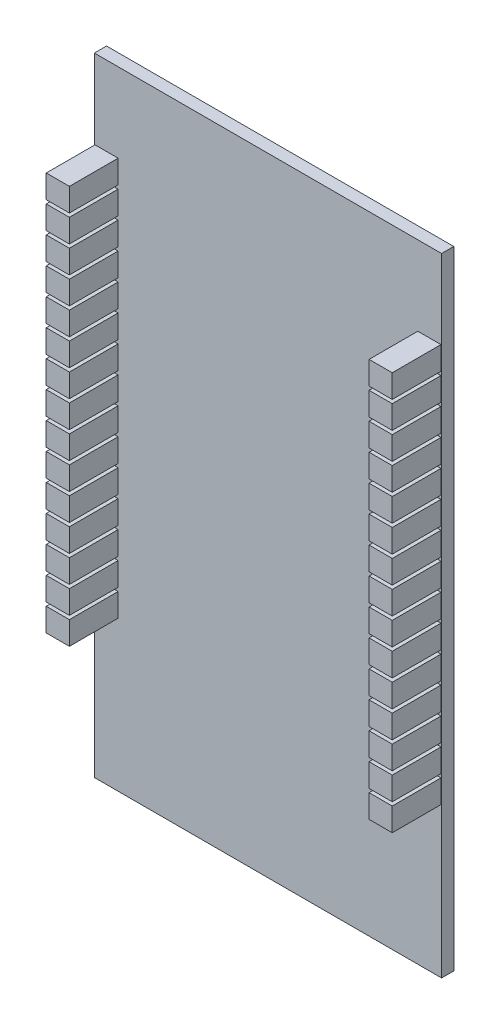
SolidWorks part; units mm, degrees
material "ﾎﾟﾘﾌﾟﾛﾋﾟﾚﾝ ﾎﾓﾎﾟﾘﾏｰ(PP Homopolymer)"
ref_plane "正面" through (0, 0, 0) normal (0, 0, 1) x (1, 0, 0)
ref_plane "平面" through (0, 0, 0) normal (0, 1, 0) x (1, 0, 0)
ref_plane "右側面" through (0, 0, 0) normal (1, 0, 0) x (0, 0, -1)
sketch "ｽｹｯﾁ1" plane through (0, 0, 0) normal (0, 0, 1) x (1, 0, 0)
  line L1 (0, 0) -> (28.5, 0)
  line L2 (0, 0) -> (0, 51.5)
  line L3 (0, 51.5) -> (28.5, 51.5)
  line L4 (28.5, 0) -> (28.5, 51.5)
  dimension "D1" = 28.5
  dimension "D2" = 51.5
extrude "ﾎﾞｽ - 押し出し1" add sketch "ｽｹｯﾁ1" along normal blind 1
sketch "ｽｹｯﾁ2" plane through (0, 0, 1) normal (0, 0, 1) x (1, 0, 0)
  line L0 (14.25, 0) -> (14.25, 51.5) construction
  line L1 (0.05, 45) -> (1.95, 45)
  line L2 (0.05, 45) -> (0.05, 43.1)
  line L3 (0.05, 43.1) -> (1.95, 43.1)
  line L4 (1.95, 45) -> (1.95, 43.1)
  line L5 (0, 51.5) -> (0, 0) construction
  line L6 (28.5, 51.5) -> (0, 51.5) construction
  line L7 (0, 0) -> (28.5, 0) construction
  line L8 (28.45, 45) -> (28.45, 43.1)
  line L9 (28.45, 43.1) -> (26.55, 43.1)
  line L10 (26.55, 45) -> (26.55, 43.1)
  line L11 (28.45, 45) -> (26.55, 45)
  line L12 (0.05, 42.8) -> (1.95, 42.8)
  line L13 (0.05, 42.8) -> (0.05, 40.9)
  line L14 (1.95, 42.8) -> (1.95, 40.9)
  line L15 (0.05, 40.9) -> (1.95, 40.9)
  line L16 (28.45, 42.8) -> (26.55, 42.8)
  line L17 (26.55, 42.8) -> (26.55, 40.9)
  line L18 (28.45, 42.8) -> (28.45, 40.9)
  line L19 (28.45, 40.9) -> (26.55, 40.9)
  line L20 (0.05, 40.6) -> (1.95, 40.6)
  line L21 (0.05, 40.6) -> (0.05, 38.7)
  line L22 (1.95, 40.6) -> (1.95, 38.7)
  line L23 (0.05, 38.7) -> (1.95, 38.7)
  line L24 (28.45, 40.6) -> (26.55, 40.6)
  line L25 (26.55, 40.6) -> (26.55, 38.7)
  line L26 (28.45, 40.6) -> (28.45, 38.7)
  line L27 (28.45, 38.7) -> (26.55, 38.7)
  line L28 (0.05, 38.4) -> (1.95, 38.4)
  line L29 (0.05, 38.4) -> (0.05, 36.5)
  line L30 (1.95, 38.4) -> (1.95, 36.5)
  line L31 (0.05, 36.5) -> (1.95, 36.5)
  line L32 (28.45, 38.4) -> (26.55, 38.4)
  line L33 (26.55, 38.4) -> (26.55, 36.5)
  line L34 (28.45, 38.4) -> (28.45, 36.5)
  line L35 (28.45, 36.5) -> (26.55, 36.5)
  line L36 (0.05, 36.2) -> (1.95, 36.2)
  line L37 (0.05, 36.2) -> (0.05, 34.3)
  line L38 (1.95, 36.2) -> (1.95, 34.3)
  line L39 (0.05, 34.3) -> (1.95, 34.3)
  line L40 (28.45, 36.2) -> (26.55, 36.2)
  line L41 (26.55, 36.2) -> (26.55, 34.3)
  line L42 (28.45, 36.2) -> (28.45, 34.3)
  line L43 (28.45, 34.3) -> (26.55, 34.3)
  line L44 (0.05, 34) -> (1.95, 34)
  line L45 (0.05, 34) -> (0.05, 32.1)
  line L46 (1.95, 34) -> (1.95, 32.1)
  line L47 (0.05, 32.1) -> (1.95, 32.1)
  line L48 (28.45, 34) -> (26.55, 34)
  line L49 (26.55, 34) -> (26.55, 32.1)
  line L50 (28.45, 34) -> (28.45, 32.1)
  line L51 (28.45, 32.1) -> (26.55, 32.1)
  line L52 (0.05, 31.8) -> (1.95, 31.8)
  line L53 (0.05, 31.8) -> (0.05, 29.9)
  line L54 (1.95, 31.8) -> (1.95, 29.9)
  line L55 (0.05, 29.9) -> (1.95, 29.9)
  line L56 (28.45, 31.8) -> (26.55, 31.8)
  line L57 (26.55, 31.8) -> (26.55, 29.9)
  line L58 (28.45, 31.8) -> (28.45, 29.9)
  line L59 (28.45, 29.9) -> (26.55, 29.9)
  line L60 (0.05, 29.6) -> (1.95, 29.6)
  line L61 (0.05, 29.6) -> (0.05, 27.7)
  line L62 (1.95, 29.6) -> (1.95, 27.7)
  line L63 (0.05, 27.7) -> (1.95, 27.7)
  line L64 (28.45, 29.6) -> (26.55, 29.6)
  line L65 (26.55, 29.6) -> (26.55, 27.7)
  line L66 (28.45, 29.6) -> (28.45, 27.7)
  line L67 (28.45, 27.7) -> (26.55, 27.7)
  line L68 (0.05, 27.4) -> (1.95, 27.4)
  line L69 (0.05, 27.4) -> (0.05, 25.5)
  line L70 (1.95, 27.4) -> (1.95, 25.5)
  line L71 (0.05, 25.5) -> (1.95, 25.5)
  line L72 (28.45, 27.4) -> (26.55, 27.4)
  line L73 (26.55, 27.4) -> (26.55, 25.5)
  line L74 (28.45, 27.4) -> (28.45, 25.5)
  line L75 (28.45, 25.5) -> (26.55, 25.5)
  line L76 (0.05, 25.2) -> (1.95, 25.2)
  line L77 (0.05, 25.2) -> (0.05, 23.3)
  line L78 (1.95, 25.2) -> (1.95, 23.3)
  line L79 (0.05, 23.3) -> (1.95, 23.3)
  line L80 (28.45, 25.2) -> (26.55, 25.2)
  line L81 (26.55, 25.2) -> (26.55, 23.3)
  line L82 (28.45, 25.2) -> (28.45, 23.3)
  line L83 (28.45, 23.3) -> (26.55, 23.3)
  line L84 (0.05, 23) -> (1.95, 23)
  line L85 (0.05, 23) -> (0.05, 21.1)
  line L86 (1.95, 23) -> (1.95, 21.1)
  line L87 (0.05, 21.1) -> (1.95, 21.1)
  line L88 (28.45, 23) -> (26.55, 23)
  line L89 (26.55, 23) -> (26.55, 21.1)
  line L90 (28.45, 23) -> (28.45, 21.1)
  line L91 (28.45, 21.1) -> (26.55, 21.1)
  line L92 (0.05, 20.8) -> (1.95, 20.8)
  line L93 (0.05, 20.8) -> (0.05, 18.9)
  line L94 (1.95, 20.8) -> (1.95, 18.9)
  line L95 (0.05, 18.9) -> (1.95, 18.9)
  line L96 (28.45, 20.8) -> (26.55, 20.8)
  line L97 (26.55, 20.8) -> (26.55, 18.9)
  line L98 (28.45, 20.8) -> (28.45, 18.9)
  line L99 (28.45, 18.9) -> (26.55, 18.9)
  line L100 (0.05, 18.6) -> (1.95, 18.6)
  line L101 (0.05, 18.6) -> (0.05, 16.7)
  line L102 (1.95, 18.6) -> (1.95, 16.7)
  line L103 (0.05, 16.7) -> (1.95, 16.7)
  line L104 (28.45, 18.6) -> (26.55, 18.6)
  line L105 (26.55, 18.6) -> (26.55, 16.7)
  line L106 (28.45, 18.6) -> (28.45, 16.7)
  line L107 (28.45, 16.7) -> (26.55, 16.7)
  line L108 (0.05, 16.4) -> (1.95, 16.4)
  line L109 (0.05, 16.4) -> (0.05, 14.5)
  line L110 (1.95, 16.4) -> (1.95, 14.5)
  line L111 (0.05, 14.5) -> (1.95, 14.5)
  line L112 (28.45, 16.4) -> (26.55, 16.4)
  line L113 (26.55, 16.4) -> (26.55, 14.5)
  line L114 (28.45, 16.4) -> (28.45, 14.5)
  line L115 (28.45, 14.5) -> (26.55, 14.5)
  line L116 (0.05, 14.2) -> (1.95, 14.2)
  line L117 (0.05, 14.2) -> (0.05, 12.3)
  line L118 (1.95, 14.2) -> (1.95, 12.3)
  line L119 (0.05, 12.3) -> (1.95, 12.3)
  line L120 (28.45, 14.2) -> (26.55, 14.2)
  line L121 (26.55, 14.2) -> (26.55, 12.3)
  line L122 (28.45, 14.2) -> (28.45, 12.3)
  line L123 (28.45, 12.3) -> (26.55, 12.3)
  dimension "D1" = 1.9
  dimension "D2" = 1.9
  dimension "D3" = 0.05
  dimension "D4" = 6.5
  dimension "D6" = 2.2
  dimension "D5" = 15
extrude "ﾎﾞｽ - 押し出し2" add sketch "ｽｹｯﾁ2" along normal blind 4 separate body
sketch "ｽｹｯﾁ3" plane through (0, 0, 0) normal (0, 0, -1) x (-1, 0, 0)
  line L0 (0, 0) -> (-28.5, 0) construction
  line L1 (-18, 0) -> (-10.5, 0)
  line L2 (-18, 0) -> (-18, 5)
  line L3 (-18, 5) -> (-10.5, 5)
  line L4 (-10.5, 0) -> (-10.5, 5)
  point P7 (-14.25, 0)
  dimension "D1" = 7.5
  dimension "D2" = 5
extrude "ﾎﾞｽ - 押し出し3" add sketch "ｽｹｯﾁ3" along normal blind 2.5 separate body
